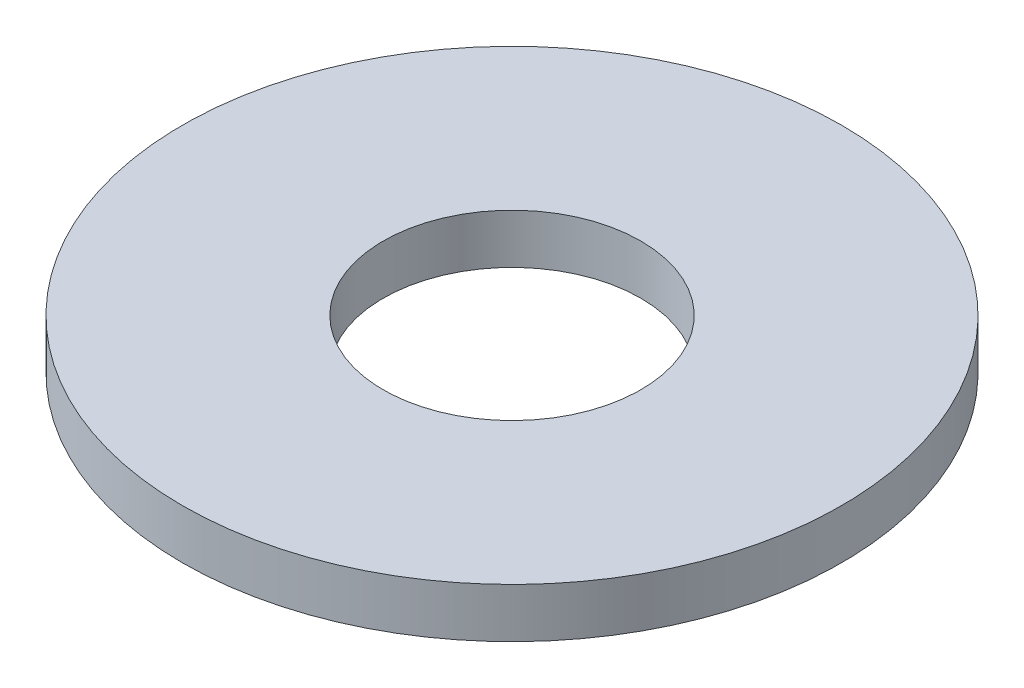
SolidWorks part; units mm, degrees
ref_plane "Front Plane" through (0, 0, 0) normal (0, 0, 1) x (1, 0, 0)
ref_plane "Top Plane" through (0, 0, 0) normal (0, 1, 0) x (1, 0, 0)
ref_plane "Right Plane" through (0, 0, 0) normal (1, 0, 0) x (0, 0, -1)
sketch "Sketch1" plane through (0, 0, 0) normal (0, 1, 0) x (1, 0, 0)
  circle A0 centre (0, 0) radius 8.4455
extrude "Boss-Extrude1" add sketch "Sketch1" along normal blind 1.27
sketch "Sketch2" plane through (0, 0, 0) normal (0, -1, 0) x (-1, 0, 0)
  circle A0 centre (0, 0) radius 3.302
extrude "Cut-Extrude1" cut sketch "Sketch2" against normal through all
